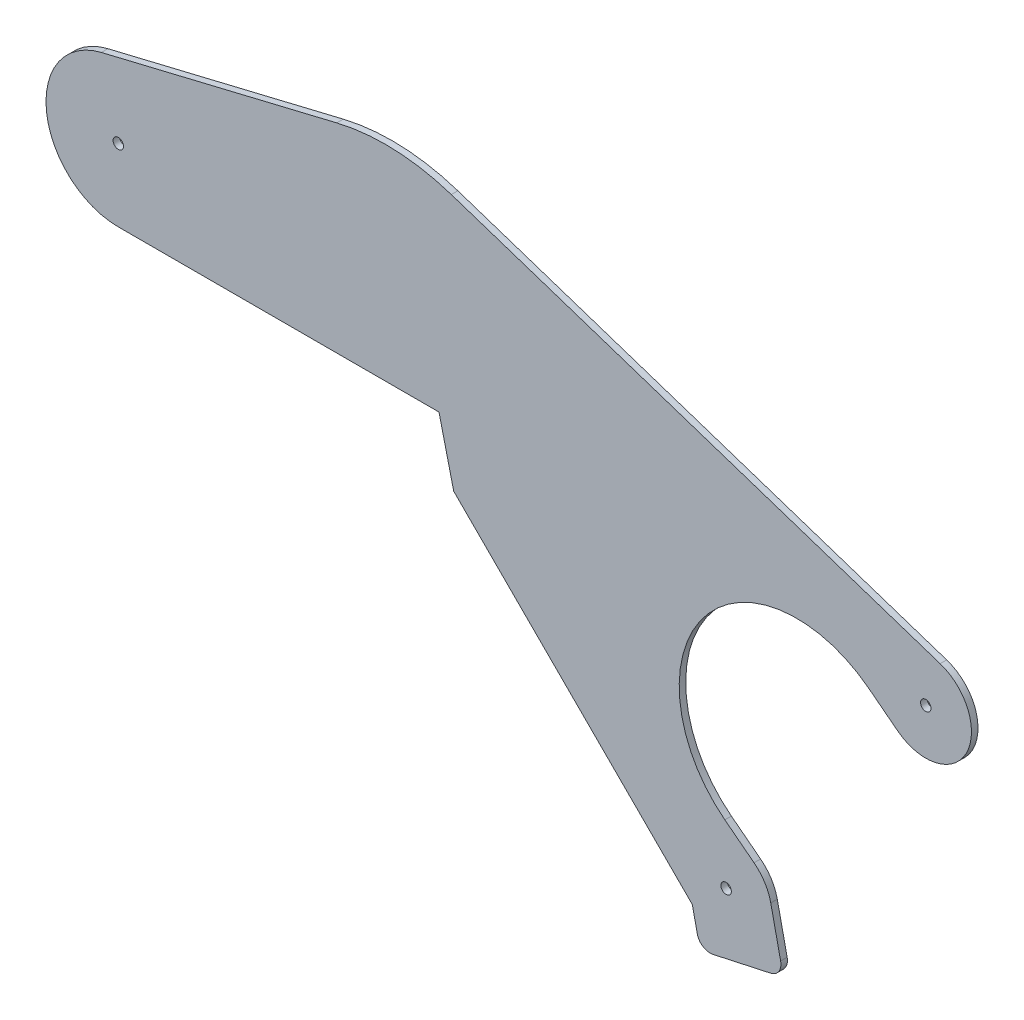
SolidWorks part; units mm, degrees
material "ABS PC"
ref_plane "Front Plane" through (0, 0, 0) normal (0, 0, 1) x (1, 0, 0)
ref_plane "Top Plane" through (0, 0, 0) normal (0, 1, 0) x (1, 0, 0)
ref_plane "Right Plane" through (0, 0, 0) normal (1, 0, 0) x (0, 0, -1)
sketch "Sketch1" plane through (0, 0, 0) normal (0, 0, 1) x (1, 0, 0)
  line L0 (0, 0) -> (0, 215.9) construction
  line L1 (133.35, 0) -> (133.35, 171.45) construction
  line L2 (0.0421, 0) -> (133.3921, 0) construction
  line L3 (50.8, 0) -> (50.8, 123.825) construction
  line L4 (508, 0) -> (508, 50000) construction
  line L11 (133.35, 171.45) -> (0, 171.45) construction
  line L20 (508, 457.2) -> (482.6, 457.2) construction
  line L22 (-203.2, 0) -> (-203.2, 53.1862) construction
  line L31 (-203.2, 520.7) -> (50.8, 520.7) construction
  line L48 (392.6736, 175.5287) -> (295.5715, 49.9391) construction
  line L49 (267.1561, 46.9237) -> (279.1404, 34.9394)
  line L50 (-8.2347, 250.0926) -> (106.2267, 277.6588)
  line L51 (161.9503, 275.3335) -> (399.6594, 196.6273)
  line L52 (0, 180.7297) -> (91.2659, 180.7297)
  line L53 (163.108, 150.9718) -> (267.1561, 46.9237)
  line L54 (309.1658, 67.5216) -> (294.957, 78.5075)
  line L55 (364.8705, 168.932) -> (379.0793, 157.9462)
  line L56 (279.1404, 34.9394) -> (281.571, 23.7819)
  line L57 (289.1272, 18.9291) -> (317.2402, 25.0535)
  line L58 (322.093, 32.6096) -> (317.2872, 54.6699)
  line L59 (91.2659, 180.7297) -> (155.9412, 180.7297)
  line L60 (155.9412, 180.7297) -> (163.108, 150.9718)
  line L61 (295.5715, 49.9391) -> (317.2872, 54.6699) construction
  circle A11 centre (508, 75.057) radius 75.057 construction
  circle A17 centre (392.6736, 175.5287) radius 28.575 construction
  circle A18 centre (295.5715, 49.9391) radius 28.575 construction
  arc A19 (-8.2347, 250.0926) -> (0, 180.7297) centre (0, 215.9) ccw
  arc A20 (317.2872, 54.6699) -> (309.1658, 67.5216) centre (295.5715, 49.9391) ccw
  arc A21 (379.0793, 157.9462) -> (399.6594, 196.6273) centre (392.6736, 175.5287) ccw
  arc A22 (294.957, 78.5075) -> (364.8705, 168.932) centre (329.9137, 123.7197) cw
  circle A23 centre (392.6736, 175.5287) radius 2.54
  circle A24 centre (295.5715, 49.9391) radius 2.54
  circle A25 centre (0, 215.9) radius 2.54
  arc A26 (317.2402, 25.0535) -> (322.093, 32.6096) centre (315.8886, 31.258) ccw
  arc A27 (281.571, 23.7819) -> (289.1272, 18.9291) centre (287.7755, 25.1335) ccw
  arc A28 (106.2267, 277.6588) -> (161.9503, 275.3335) centre (130.0152, 178.8829) cw
  point P17 (-177.8, 889)
  point P19 (175.5516, 255.7613)
  point P24 (313.0499, 72.5452)
  point P27 (287.5936, 18.595)
  point P29 (175.4179, 247.041)
  point P38 (134.4204, 284.4487)
  point P42 (133.35, 180.7297)
  point P43 (-3.1011, 429.5183)
  point P48 (161.9166, 189.1642)
  point P49 (0, 0)
  point P51 (167.8816, 293.6989)
  point P52 (171.4042, 273.5153)
  point P55 (168.0197, 293.1104)
  point P56 (163.5071, 316.4158)
  point P57 (165.5882, 302.3818)
  point P58 (0, 0)
  point P59 (0, 0)
  point P60 (0, 0)
  point P71 (309.9426, 68.5264)
  dimension "D4" = 304.8
  dimension "D9" = 57.15
  dimension "D10" = 133.35
  dimension "D12" = 5.08
  dimension "D13" = 150.114
  dimension "D14" = 22.225
  dimension "D21" = 114.3
  dimension "D3" = 171.45
  dimension "D6" = 57.15
  dimension "D15" = 22.225
  dimension "D25" = 64.6753
  dimension "D23" = 189.2304
  dimension "D8" = 69.85
  dimension "D16" = 114.3
  dimension "D22" = 279.4
  dimension "D28" = 5.08
  dimension "D29" = 6.35
  dimension "D30" = 101.6
  dimension "D1" = 82.55
  dimension "D2" = 215.9
  dimension "D5" = 50.8
  dimension "D7" = 457.2
  dimension "D17" = 457.2
  dimension "D18" = 177.8
  dimension "D19" = 889
  dimension "D20" = 25.4
  dimension "D24" = 135
  dimension "4.5" = 203.2
  dimension "D26" = 41.4724
  dimension "D27" = 18.401
  dimension "D31" = 30.6088
  dimension "D32" = 103.541
  dimension "D33" = 13.541
  dimension "D34" = 11.4191
  dimension "D35" = 22.5776
  dimension "D36" = 40
  dimension "D37" = 147.29
  dimension "D38" = 140
  dimension "D39" = 148.139
extrude "Boss-Extrude1" add sketch "Sketch1" along normal blind 3.175
